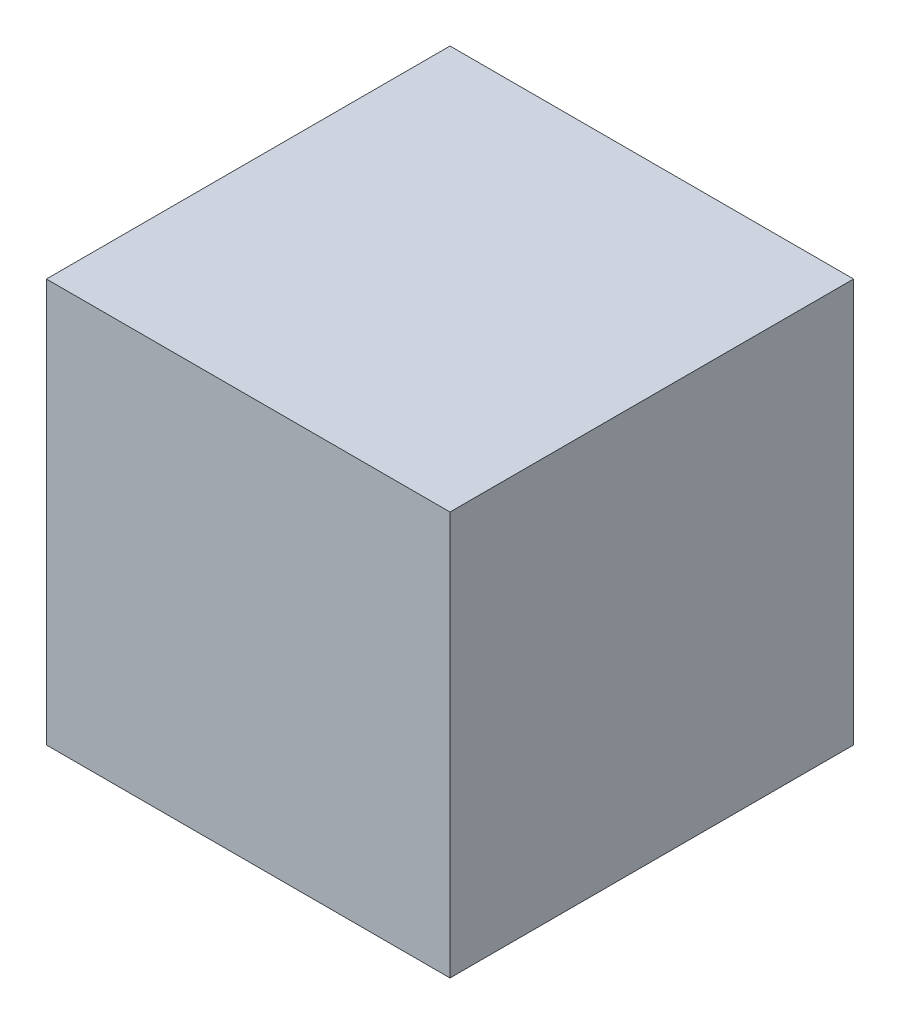
SolidWorks part; units mm, degrees
ref_plane "Front Plane" through (0, 0, 0) normal (0, 0, 1) x (1, 0, 0)
ref_plane "Top Plane" through (0, 0, 0) normal (0, 1, 0) x (1, 0, 0)
ref_plane "Right Plane" through (0, 0, 0) normal (1, 0, 0) x (0, 0, -1)
sketch "Sketch3" plane through (0, 0, 0) normal (0, 1, 0) x (1, 0, 0)
  line L1 (0, 0) -> (-19.05, 0)
  line L2 (0, 0) -> (0, 19.05)
  line L3 (0, 19.05) -> (-19.05, 19.05)
  line L4 (-19.05, 0) -> (-19.05, 19.05)
  dimension "D1" = 19.05
  dimension "D2" = 19.05
extrude "Boss-Extrude1" add sketch "Sketch3" along normal blind 19.05
